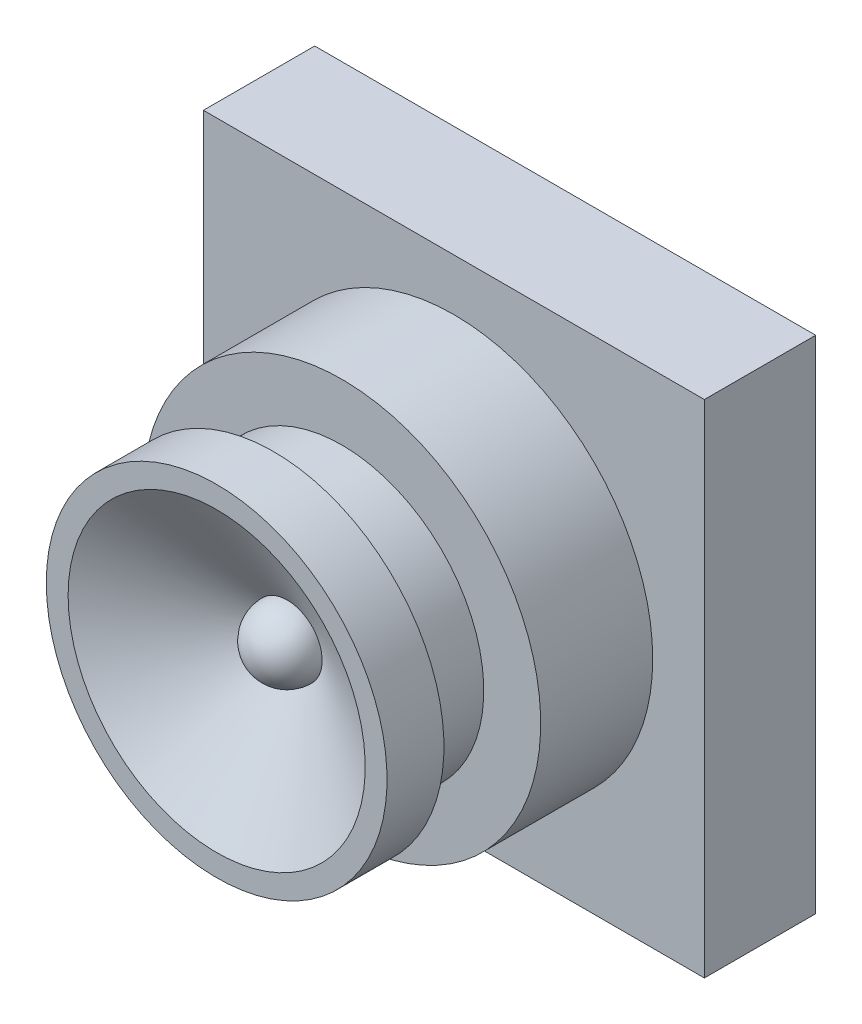
SolidWorks part; units mm, degrees
ref_plane "Plan de face" through (0, 0, 0) normal (0, 0, 1) x (1, 0, 0)
ref_plane "Plan de dessus" through (0, 0, 0) normal (0, 1, 0) x (1, 0, 0)
ref_plane "Plan de droite" through (0, 0, 0) normal (1, 0, 0) x (0, 0, -1)
sketch "Esquisse1" plane through (0, 0, 0) normal (0, 0, 1) x (1, 0, 0)
  line L1 (-9, 9) -> (9, 9)
  line L2 (-9, 9) -> (-9, -9)
  line L3 (-9, -9) -> (9, -9)
  line L4 (9, 9) -> (9, -9)
  dimension "D1" = 18
  dimension "D2" = 18
  dimension "D3" = 9
  dimension "D4" = 9
extrude "Extrusion1" add sketch "Esquisse1" along normal blind 4
sketch "Esquisse2" plane through (0, 0, 0) normal (0, 1, 0) x (1, 0, 0)
  line L0 (0, 0) -> (0, -16.5947) construction
  line L1 (0, -4) -> (-7.1437, -4)
  line L2 (9, -4) -> (-9, -4) construction
  line L3 (-7.1437, -4) -> (-7.1437, -8.0247)
  line L4 (-7.1437, -8.0247) -> (-5.0987, -8.0247)
  line L5 (-5.0987, -8.0247) -> (-5.0987, -9.9878)
  line L6 (-5.0987, -9.9878) -> (-4.5534, -9.9878)
  line L7 (-4.5534, -9.9878) -> (-4.5534, -10.4786)
  line L8 (-4.5534, -10.4786) -> (-6.1212, -10.4786)
  line L9 (-6.1212, -10.4786) -> (-6.1212, -12.5236)
  line L10 (-6.1212, -12.5236) -> (-5.3373, -12.5236)
  line L11 (-5.3373, -12.5236) -> (-1.2542, -9.9878)
  line L12 (0, -11.2557) -> (0, -4)
  arc A0 (-1.2542, -9.9878) -> (0, -11.2557) centre (0.0068, -9.9946) ccw
revolve "Révolution1" add sketch "Esquisse2" angle 360 about L0
